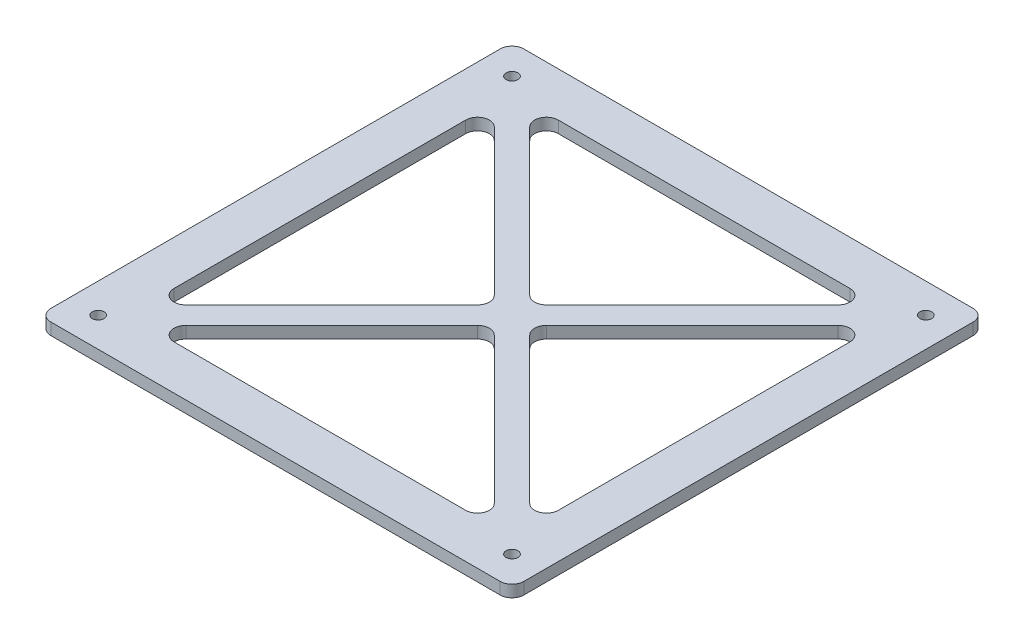
SolidWorks part; units mm, degrees
ref_plane "前基準面" through (0, 0, 0) normal (0, 0, 1) x (1, 0, 0)
ref_plane "上基準面" through (0, 0, 0) normal (0, 1, 0) x (1, 0, 0)
ref_plane "右基準面" through (0, 0, 0) normal (1, 0, 0) x (0, 0, -1)
ref_plane "平面1" through (0, 3, 0) normal (0, 1, 0) x (1, 0, 0)
sketch "草圖1" plane through (0, 3, 0) normal (0, 1, 0) x (1, 0, 0)
  line L0 (-60, 57) -> (-60, -57)
  line L1 (-57, -60) -> (57, -60)
  line L2 (60, -57) -> (60, 57)
  line L3 (57, 60) -> (-57, 60)
  line L4 (43.6287, -39.1287) -> (6.6213, -2.1213)
  line L5 (6.6213, 2.1213) -> (43.6287, 39.1287)
  line L6 (48.75, 37.0074) -> (48.75, -37.0074)
  line L7 (39.1287, 43.6287) -> (2.1213, 6.6213)
  line L8 (-2.1213, 6.6213) -> (-39.1287, 43.6287)
  line L9 (-37.0074, 48.75) -> (37.0074, 48.75)
  line L10 (-39.1287, -43.6287) -> (-2.1213, -6.6213)
  line L11 (2.1213, -6.6213) -> (39.1287, -43.6287)
  line L12 (37.0074, -48.75) -> (-37.0074, -48.75)
  line L13 (-48.75, -37.0074) -> (-48.75, 37.0074)
  line L14 (-43.6287, 39.1287) -> (-6.6213, 2.1213)
  line L15 (-6.6213, -2.1213) -> (-43.6287, -39.1287)
  arc A0 (-60, -57) -> (-57, -60) centre (-57, -57) ccw
  arc A1 (57, -60) -> (60, -57) centre (57, -57) ccw
  arc A2 (60, 57) -> (57, 60) centre (57, 57) ccw
  arc A3 (-57, 60) -> (-60, 57) centre (-57, 57) ccw
  arc A4 (6.6213, -2.1213) -> (6.6213, 2.1213) centre (8.7426, 0) cw
  arc A5 (43.6287, 39.1287) -> (48.75, 37.0074) centre (45.75, 37.0074) cw
  arc A6 (48.75, -37.0074) -> (43.6287, -39.1287) centre (45.75, -37.0074) cw
  arc A7 (2.1213, 6.6213) -> (-2.1213, 6.6213) centre (0, 8.7426) cw
  arc A8 (-39.1287, 43.6287) -> (-37.0074, 48.75) centre (-37.0074, 45.75) cw
  arc A9 (37.0074, 48.75) -> (39.1287, 43.6287) centre (37.0074, 45.75) cw
  arc A10 (-2.1213, -6.6213) -> (2.1213, -6.6213) centre (0, -8.7426) cw
  arc A11 (39.1287, -43.6287) -> (37.0074, -48.75) centre (37.0074, -45.75) cw
  arc A12 (-37.0074, -48.75) -> (-39.1287, -43.6287) centre (-37.0074, -45.75) cw
  arc A13 (-48.75, 37.0074) -> (-43.6287, 39.1287) centre (-45.75, 37.0074) cw
  arc A14 (-6.6213, 2.1213) -> (-6.6213, -2.1213) centre (-8.7426, 0) cw
  arc A15 (-43.6287, -39.1287) -> (-48.75, -37.0074) centre (-45.75, -37.0074) cw
  circle A16 centre (52.5, -52.5) radius 1.5
  circle A17 centre (-52.5, 52.5) radius 1.5
  circle A18 centre (52.5, 52.5) radius 1.5
  circle A19 centre (-52.5, -52.5) radius 1.5
extrude "填料-伸長1" add sketch "草圖1" against normal blind 3
